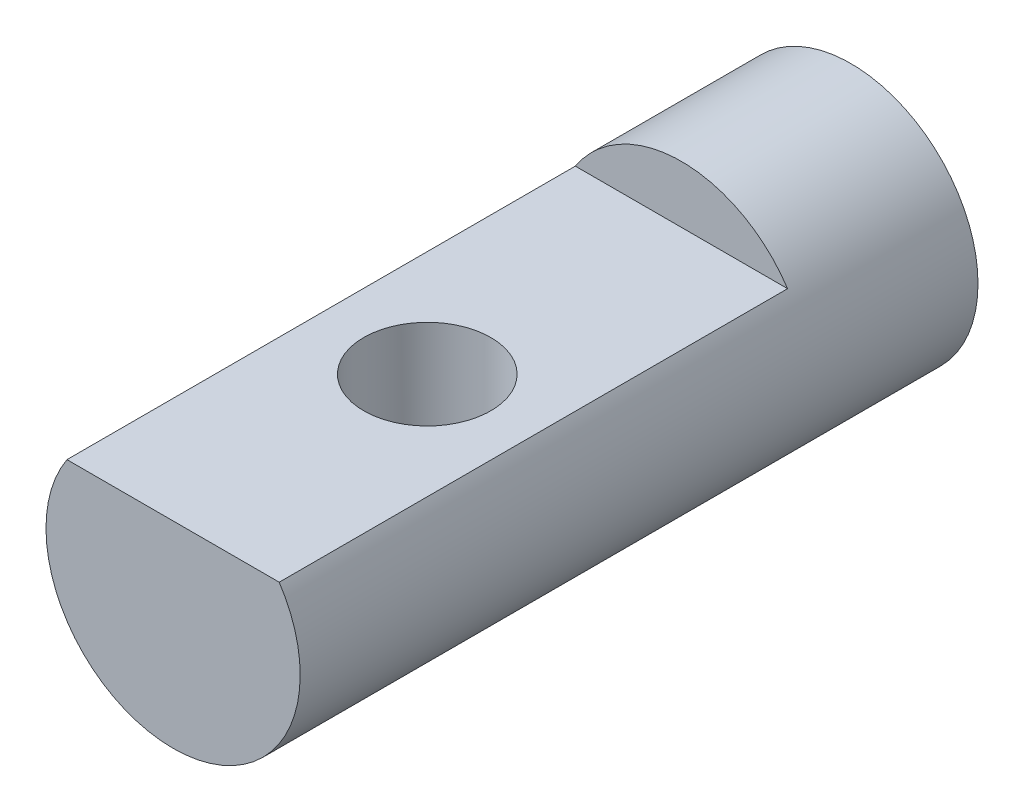
SolidWorks part; units mm, degrees
ref_plane "Front Plane" through (0, 0, 0) normal (0, 0, 1) x (1, 0, 0)
ref_plane "Top Plane" through (0, 0, 0) normal (0, 1, 0) x (1, 0, 0)
ref_plane "Right Plane" through (0, 0, 0) normal (1, 0, 0) x (0, 0, -1)
sketch "Sketch1" plane through (0, 0, 0) normal (0, 0, 1) x (1, 0, 0)
  circle A0 centre (0, 0) radius 3
  dimension "D1" = 6
extrude "Boss-Extrude1" add sketch "Sketch1" along normal blind 16
sketch "Sketch2" plane through (0, 0, 16) normal (0, 0, 1) x (1, 0, 0)
  line L0 (0, 3) -> (0, 1.65) construction
  line L1 (-2.5055, 1.65) -> (2.5055, 1.65)
  circle A0 centre (0, 0) radius 3 construction
  arc A1 (2.5055, 1.65) -> (-2.5055, 1.65) centre (0, 0) ccw
  point P9 (0, 1.65)
  dimension "D1" = 1.35
extrude "Cut-Extrude1" cut sketch "Sketch2" against normal blind 12
sketch "Sketch3" plane through (0, 1.65, 0) normal (0, 1, 0) x (1, 0, 0)
  line L0 (0, -4) -> (0, -16) construction
  line L1 (-2.5055, -4) -> (2.5055, -4) construction
  line L2 (-2.5055, -16) -> (2.5055, -16) construction
  circle A0 centre (0, -10) radius 1.5
  dimension "D1" = 3
extrude "Cut-Extrude2" cut sketch "Sketch3" against normal blind 12
